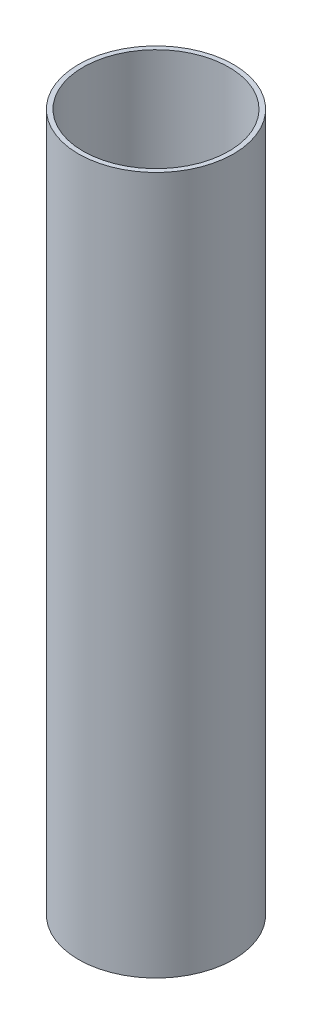
SolidWorks part; units mm, degrees
ref_plane "Front Plane" through (0, 0, 0) normal (0, 0, 1) x (1, 0, 0)
ref_plane "Top Plane" through (0, 0, 0) normal (0, 1, 0) x (1, 0, 0)
ref_plane "Right Plane" through (0, 0, 0) normal (1, 0, 0) x (0, 0, -1)
sketch "Sketch1" plane through (0, 0, 0) normal (0, 1, 0) x (1, 0, 0)
  circle A0 centre (0, 0) radius 6.35
  circle A1 centre (0, 0) radius 5.969
  dimension "D1" = 12.7
  dimension "D2" = 11.938
extrude "Boss-Extrude1" add sketch "Sketch1" along normal blind 57.15
